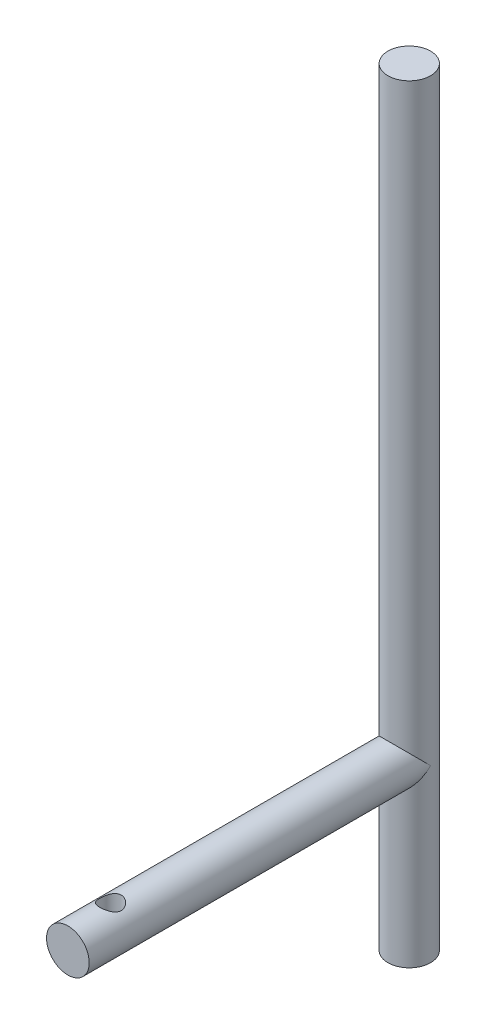
SolidWorks part; units mm, degrees
ref_plane "Front Plane" through (0, 0, 0) normal (0, 0, 1) x (1, 0, 0)
ref_plane "Top Plane" through (0, 0, 0) normal (0, 1, 0) x (1, 0, 0)
ref_plane "Right Plane" through (0, 0, 0) normal (1, 0, 0) x (0, 0, -1)
sketch "Sketch1" plane through (0, 0, 0) normal (0, 1, 0) x (1, 0, 0)
  circle A0 centre (0, 0) radius 3.175
  dimension "D1" = 6.35
extrude "Boss-Extrude1" add sketch "Sketch1" along normal blind 114.3
sketch "Sketch2" plane through (0, 0, 0) normal (0, 0, 1) x (1, 0, 0)
  line L0 (-3.175, 0) -> (-3.175, 114.3)
  line L1 (3.175, 114.3) -> (3.175, 0)
  line L2 (3.175, 114.3) -> (3.175, 0) construction
  line L3 (-3.175, 0) -> (-3.175, 114.3) construction
  circle A0 centre (0, 25.4) radius 3.175
  dimension "D2" = 6.35
  dimension "D1" = 25.4
extrude "Boss-Extrude2" add sketch "Sketch2" along normal blind 50.8
sketch "Sketch3" plane through (0, 0, 0) normal (0, 1, 0) x (1, 0, 0)
  line L0 (-3.175, -50.8) -> (3.175, -50.8) construction
  line L1 (-3.175, -50.8) -> (3.175, -50.8) construction
  circle A0 centre (0, -44.45) radius 1.5875
  point P4 (0, -50.8)
  dimension "D1" = 3.175
  dimension "D2" = 6.35
extrude "Cut-Extrude1" cut sketch "Sketch3" along normal through all
